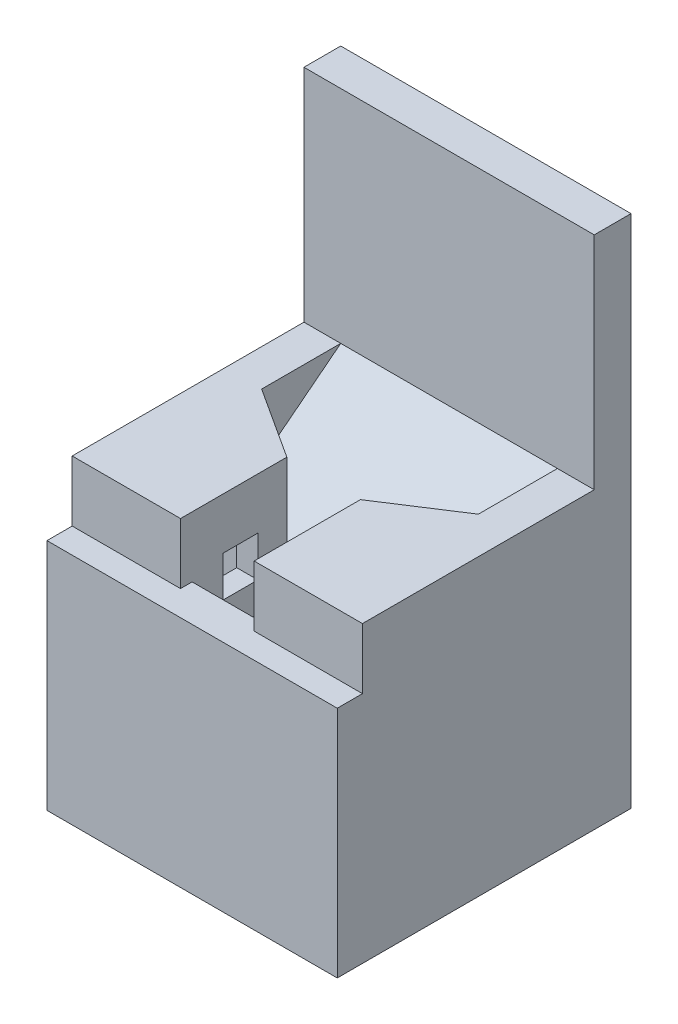
SolidWorks part; units mm, degrees
ref_plane "Front Plane" through (0, 0, 0) normal (0, 0, 1) x (1, 0, 0)
ref_plane "Top Plane" through (0, 0, 0) normal (0, 1, 0) x (1, 0, 0)
ref_plane "Right Plane" through (0, 0, 0) normal (1, 0, 0) x (0, 0, -1)
sketch "Sketch2" plane through (0, 0, 0) normal (0, 1, 0) x (1, 0, 0)
  line L1 (-9.35, 10) -> (9.35, 10)
  line L2 (-9.35, 10) -> (-9.35, -10)
  line L3 (-9.35, -10) -> (9.35, -10)
  line L4 (9.35, 10) -> (9.35, -10)
  point P4 (0, 10)
  point P6 (-9.35, 0)
  dimension "D1" = 18.7
  dimension "D2" = 20
extrude "Boss-Extrude1" add sketch "Sketch2" along normal blind 25.4
sketch "Sketch3" plane through (0, 0, -10) normal (0, 0, -1) x (-1, 0, 0)
  line L0 (-9.35, 25.4) -> (9.35, 25.4) construction
  line L1 (-3.175, 25.4) -> (3.175, 25.4)
  line L2 (-3.175, 25.4) -> (-3.175, 18.1)
  line L3 (-3.175, 18.1) -> (3.175, 18.1)
  line L4 (3.175, 25.4) -> (3.175, 18.1)
  line L5 (-9.35, 22.225) -> (9.35, 22.225) construction
  line L6 (-9.35, 25.4) -> (-9.35, 0) construction
  line L7 (9.35, 25.4) -> (9.35, 0) construction
  line L9 (-3.175, 18.1) -> (3.175, 18.1)
  line L10 (-3.175, 18.1) -> (-3.175, 14.925)
  line L11 (-3.175, 14.925) -> (3.175, 14.925)
  line L12 (3.175, 18.1) -> (3.175, 14.925)
  point P6 (0, 18.1)
  point P9 (6.0716, 19.725)
  line M12 (9.35, 25.4) -> (-9.35, 25.4)
  dimension "D1" = 6.35
  dimension "D2" = 3.175
  dimension "D3" = 2.5
  dimension "D4" = 1.625
  dimension "D5" = 3.175
extrude "Cut-Extrude1" cut sketch "Sketch3" against normal through all contours L12 L3 L10 L11 | L5 L2 L3 L4 | L2 L5 L4 M12
sketch "Sketch5" plane through (0, 0, -10) normal (0, 0, -1) x (-1, 0, 0)
  line L0 (9.35, 25.4) -> (9.35, 0) construction
  line L1 (-9.35, 25.4) -> (-12.525, 25.4)
  line L2 (-9.35, 25.4) -> (-9.35, 0)
  line L3 (-9.35, 0) -> (-12.525, 0)
  line L4 (-12.525, 25.4) -> (-12.525, 0)
  line L5 (9.35, 25.4) -> (12.525, 25.4)
  line L6 (9.35, 25.4) -> (9.35, 0)
  line L7 (9.35, 0) -> (12.525, 0)
  line L8 (12.525, 25.4) -> (12.525, 0)
  line L9 (-9.35, 0) -> (9.35, 0) construction
  dimension "D1" = 3.175
extrude "Boss-Extrude2" add sketch "Sketch5" against normal up to surface (20 mm away) up to face at (0, 16.4312, 10)
sketch "Sketch6" plane through (0, 0, -10) normal (0, 0, -1) x (-1, 0, 0)
  line L0 (-12.525, 0) -> (12.525, 0) construction
  line L1 (-9.35, 22.225) -> (-5, 22.225)
  line L2 (-9.35, 22.225) -> (-9.35, 0)
  line L3 (-9.35, 0) -> (-5, 0)
  line L4 (-5, 22.225) -> (-5, 0)
  line L5 (-3.175, 14.925) -> (3.175, 14.925) construction
  line L6 (-5, 10.125) -> (5, 10.125)
  line L7 (-5, 10.125) -> (-5, 0)
  line L8 (-5, 0) -> (5, 0)
  line L9 (5, 10.125) -> (5, 0)
  line L10 (9.35, 0) -> (5, 0)
  line L11 (9.35, 0) -> (9.35, 22.225)
  line L12 (9.35, 22.225) -> (5, 22.225)
  line L13 (5, 0) -> (5, 22.225)
  line L14 (-12.525, 25.4) -> (-3.175, 25.4) construction
  point P12 (0, 10.125)
  point P15 (0, 14.925)
  line M18 (-12.525, 0) -> (12.525, 0)
  dimension "D1" = 10
  dimension "D2" = 18.7
  dimension "D3" = 3.175
  dimension "D4" = 12.1
extrude "Cut-Extrude2" cut sketch "Sketch6" against normal blind 16.825 contours L13 L9 L11 L12 M18 | L9 L6 L4 M18 | L4 L1 L2 M18
sketch "Sketch7" plane through (5, 0, 0) normal (1, 0, 0) x (0, 0, -1)
  line L0 (-6.825, 22.225) -> (-6.825, 10.125) construction
  line L1 (-6.325, 20.975) -> (-3.325, 20.975)
  line L2 (-6.325, 20.975) -> (-6.325, 17.475)
  line L3 (-6.325, 17.475) -> (-3.325, 17.475)
  line L4 (-3.325, 20.975) -> (-3.325, 17.475)
  line L5 (-6.825, 22.225) -> (10, 22.225) construction
  point P6 (-4.825, 17.475)
  point P7 (-6.325, 19.225)
  dimension "D1" = 3
  dimension "D2" = 2
  dimension "D3" = 3
  dimension "D4" = 3.5
extrude "Cut-Extrude3" cut sketch "Sketch7" against normal up to surface (10 mm away) up to face at (-5, 16.175, -1.5875)
sketch "Sketch8" plane through (0, 0, -10) normal (0, 0, -1) x (-1, 0, 0)
  line L0 (9.35, 0) -> (12.525, 0) construction
  line L1 (-11, 10.125) -> (11, 10.125)
  line L2 (-11, 10.125) -> (-11, 0)
  line L3 (-11, 0) -> (11, 0)
  line L4 (11, 10.125) -> (11, 0)
  line L5 (-5, 10.125) -> (5, 10.125) construction
  point P9 (0, 10.125)
  dimension "D1" = 22
extrude "Cut-Extrude4" cut sketch "Sketch8" against normal blind 19
sketch "Sketch10" plane through (12.525, 0, 0) normal (1, 0, 0) x (0, 0, -1)
  line L1 (-12.175, 20.1625) -> (-9, 20.1625)
  line L2 (-12.175, 20.1625) -> (-12.175, 0)
  line L3 (-12.175, 0) -> (-9, 0)
  line L4 (-9, 20.1625) -> (-9, 0)
  line L5 (-10, 25.4) -> (-10, 14.925) construction
  point P4 (-9, 21.42)
  point P8 (-9, 17.5273)
  point P9 (-10, 20.1625)
  dimension "D1" = 3.175
extrude "Boss-Extrude3" add sketch "Sketch10" against normal up to surface (25.05 mm away) up to face at (-12.525, 12.7, 0)
sketch "Sketch11" plane through (12.525, 0, 0) normal (1, 0, 0) x (0, 0, -1)
  line L0 (-0.825, 12.9102) -> (10, 21.3704)
  line L3 (-12.175, 0) -> (10, 0) construction
  line L4 (10, 25.4) -> (-0.825, 16.9398)
  line L5 (-0.825, 16.9398) -> (-0.825, 12.9102)
  line L7 (10, 25.4) -> (10, 44.45)
  line L8 (10, 44.45) -> (13.175, 44.45)
  line L9 (13.175, 44.45) -> (13.175, 0)
  line L10 (13.175, 0) -> (10, 0)
  line L11 (10, 0) -> (10, 21.3704)
  line L12 (10, 25.4) -> (10, 21.3704)
  line L13 (-10, 25.4) -> (10, 25.4) construction
  line L14 (10, 25.4) -> (10, 0) construction
  line L15 (-9, 14.925) -> (10, 14.925) construction
  line L16 (-6.825, 22.225) -> (-6.825, 10.125) construction
  point P29 (-0.825, 14.925)
  line M10 (10, 0) -> (10, 25.4)
  dimension "D1" = 6
  dimension "D2" = 3.175
  dimension "D3" = 3.175
  dimension "D4" = 44.45
extrude "Boss-Extrude10" add sketch "Sketch11" against normal up to surface (25.05 mm away) contours L4 L5 L0 M10 | L10 L9 L8 L7 M10 up to face at (-12.525, 15.1875, 4.0583)
sketch "Sketch12" plane through (0, 25.4, 0) normal (0, 1, 0) x (1, 0, 0)
  line L0 (-3.175, 10) -> (-12.525, 10) construction
  line L1 (-9.35, 10) -> (9.35, 10)
  line L2 (-9.35, 10) -> (-9.35, -0.825)
  line L3 (-9.35, -0.825) -> (9.35, -0.825)
  line L4 (9.35, 10) -> (9.35, -0.825)
  line L5 (-3.175, -0.825) -> (3.175, -0.825) construction
  line L6 (12.525, -10) -> (12.525, 10) construction
  line L7 (-3.175, -0.825) -> (-9.35, 3.175)
  line L8 (-3.175, -10) -> (-3.175, 10) construction
  line L9 (9.35, 3.175) -> (3.175, -0.825)
  line L10 (3.175, -10) -> (3.175, 10) construction
  point P8 (0, -0.825)
  point P9 (0, -0.825)
  dimension "D1" = 3.175
  dimension "D2" = 4
extrude "Cut-Extrude5" cut sketch "Sketch12" against normal up to surface
sketch "Sketch13" plane through (0, 25.4, 0) normal (0, 1, 0) x (1, 0, 0)
  line L0 (-9.35, 3.175) -> (-9.35, -0.825)
  line L4 (-3.175, -0.825) -> (-9.35, 3.175)
  line L5 (9.35, 3.175) -> (9.35, -0.825)
  line L6 (3.175, -0.825) -> (9.35, 3.175)
  line L9 (9.35, -0.825) -> (3.175, -0.825)
  line L11 (-3.175, -0.825) -> (-9.35, -0.825)
  line L12 (-9.35, -0.825) -> (-5, -0.825) construction
  point P4 (0, 0)
extrude "Boss-Extrude11" add sketch "Sketch13" against normal up to surface (5.334 mm away)
